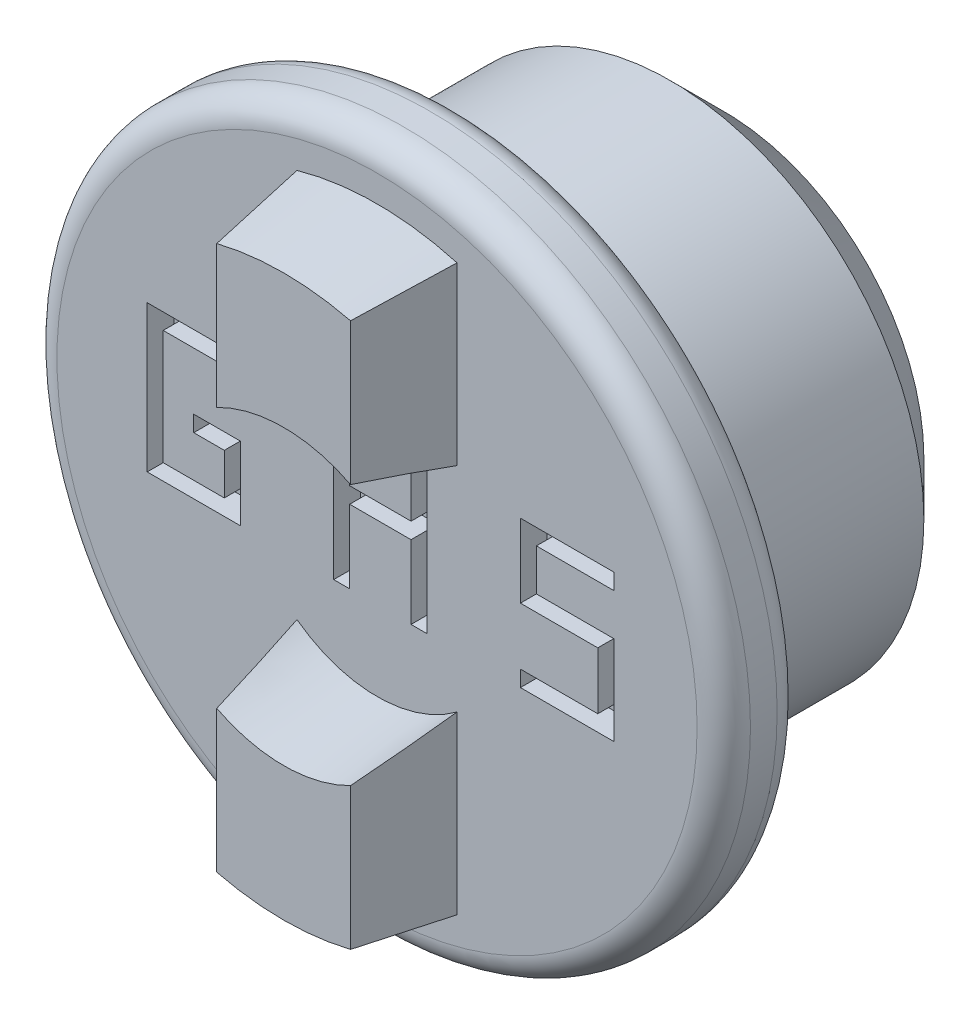
SolidWorks part; units mm, degrees
ref_plane "Front Plane" through (0, 0, 0) normal (0, 0, 1) x (1, 0, 0)
ref_plane "Top Plane" through (0, 0, 0) normal (0, 1, 0) x (1, 0, 0)
ref_plane "Right Plane" through (0, 0, 0) normal (1, 0, 0) x (0, 0, -1)
sketch "Sketch1" plane through (0, 0, 0) normal (0, 0, 1) x (1, 0, 0)
  circle A0 centre (0, 0) radius 9.5
  dimension "D1" = 19
extrude "Boss-Extrude1" add sketch "Sketch1" along normal blind 10
chamfer "Chamfer1" distance 2 angle 45 1 edges at (9.5, 0, 0)
sketch "Sketch2" plane through (0, 0, 10) normal (0, 0, 1) x (1, 0, 0)
  circle A0 centre (0, 0) radius 13
  dimension "D1" = 26
extrude "Boss-Extrude2" add sketch "Sketch2" along normal blind 3
sketch "Sketch4" plane through (0, 0, 13) normal (0, 0, 1) x (1, 0, 0)
  line L0 (0, 13.5071) -> (0, 5) construction
  line L1 (3, 10.583) -> (3, 4)
  line L2 (-3, 10.583) -> (-3, 4)
  line L3 (3, -4) -> (3, -10.583)
  line L4 (0, -5) -> (0, -14.5643) construction
  line L5 (-3, -4) -> (-3, -10.583)
  arc A1 (-3, -4) -> (3, -4) centre (0, 0) ccw
  circle A2 centre (0, 0) radius 5
  circle A3 centre (0, 0) radius 11
  arc A4 (3, 10.583) -> (-3, 10.583) centre (0, 0) ccw
  arc A5 (3, 4) -> (-3, 4) centre (0, 0) ccw
  arc A6 (-3, -10.583) -> (3, -10.583) centre (0, 0) ccw
  dimension "D3" = 6
  dimension "D1" = 2
  dimension "D2" = 8
extrude "Boss-Extrude3" add sketch "Sketch4" along normal blind 3.5 draft 8
sketch "Sketch5" plane through (0, 0, 16.5) normal (0, 0, 1) x (1, 0, 0)
  line L14 (-17.9352, 0) -> (20.3888, 0) construction
fillet "Fillet1" radius 1 2 edges at (13, 0, 10) (13, 0, 13)
sketch "Sketch3" plane through (0, 0, 13) normal (0, 0, 1) x (1, 0, 0)
  line L0 (-14.7284, 0) -> (19.3583, 0) construction
  line L1 (-1.6251, -2.0139) -> (-1.6251, 3.4803)
  line L2 (-1.6251, 3.4803) -> (1.8749, 3.4803)
  line L21 (1.8749, 3.4803) -> (1.8749, -2.0197)
  line L22 (1.8749, -2.0197) -> (1.2749, -2.0197)
  line L23 (1.2749, -2.0197) -> (1.2749, 0.7322)
  line L24 (1.2749, 0.7322) -> (-1.0251, 0.7322)
  line L25 (-1.0251, 0.7322) -> (-1.0251, -2.0139)
  line L26 (-1.0251, -2.0139) -> (-1.6251, -2.0139)
  line L27 (-1.0251, -2.0139) -> (-1.0251, 0.7322)
  line L28 (-1.0251, 2.8803) -> (1.2749, 2.8803)
  line L29 (1.2749, 2.8803) -> (1.2749, 1.3322)
  line L30 (1.2749, 1.3322) -> (-1.0251, 1.3322)
  line L31 (1.2749, 1.3322) -> (-1.0251, 1.3322) construction
  line L32 (5.3749, 3.4803) -> (8.8749, 3.4803)
  line L33 (1.2749, 2.8803) -> (1.2749, -2.0197) construction
  line L34 (-1.0251, 1.3322) -> (-1.0251, 2.8803)
  line L35 (-1.0251, -2.0139) -> (-1.0251, 2.8803) construction
  line L36 (5.3749, 3.4803) -> (5.3749, 0.7209)
  line L37 (5.3749, 0.7209) -> (8.2749, 0.7209)
  line L38 (8.2749, 0.7209) -> (8.2749, -1.4197)
  line L39 (8.2749, -1.4197) -> (5.3749, -1.4197)
  line L40 (8.8749, 1.3209) -> (8.8749, -1.4197)
  line L41 (5.9749, 1.3209) -> (8.8749, 1.3209)
  line L42 (5.9749, 2.8803) -> (5.9749, 1.3209)
  line L43 (5.9749, 2.8803) -> (8.8749, 2.8803)
  line L44 (8.8749, 2.8803) -> (8.8749, 3.4803)
  line L45 (8.8749, -1.4197) -> (8.8749, -2.0197)
  line L46 (8.8749, -2.0197) -> (5.3749, -2.0197)
  line L47 (5.3749, -2.0197) -> (5.3749, -1.4197)
  line L48 (-8.6155, 3.4803) -> (-8.6155, -2.0139)
  line L49 (-8.6155, -2.0139) -> (-5.1251, -2.0139)
  line L50 (-5.1251, -2.0139) -> (-5.1251, 0.7332)
  line L51 (-5.1251, 0.7332) -> (-6.8703, 0.7332)
  line L52 (-8.6155, 3.4803) -> (-5.1251, 3.4803)
  line L53 (-5.7251, 0.1332) -> (-6.8703, 0.1332)
  line L54 (-5.7251, -1.4139) -> (-5.7251, 0.1332)
  line L55 (-8.0155, -1.4139) -> (-5.7251, -1.4139)
  line L56 (-8.0155, 2.8803) -> (-8.0155, -1.4139)
  line L57 (-8.0155, 2.8803) -> (-5.1251, 2.8803)
  line L58 (-5.1251, 3.4803) -> (-5.1251, 2.8803)
  line L59 (-6.8703, 0.1332) -> (-6.8703, 0.7332)
  line L60 (-3, 10.583) -> (-3, 4) construction
  dimension "D4" = 0.6
  dimension "D5" = 0.6
  dimension "D1" = 0.6
  dimension "D2" = 5.5
  dimension "D6" = 3.5
  dimension "D7" = 0.6
  dimension "D8" = 3.5
  dimension "D9" = 3.5
  dimension "D10" = 2.3749
  dimension "D11" = 8.1251
  dimension "D12" = 11.6155
  dimension "D13" = 7.1027
  dimension "D3" = 3.5
  dimension "D14" = 9.8498
  dimension "D15" = 9.8508
  dimension "D16" = 9.8621
  dimension "D17" = 12.5969
  dimension "D18" = 2.1406
  dimension "D19" = 1.7452
extrude "Cut-Extrude1" cut sketch "Sketch3" against normal blind 1
